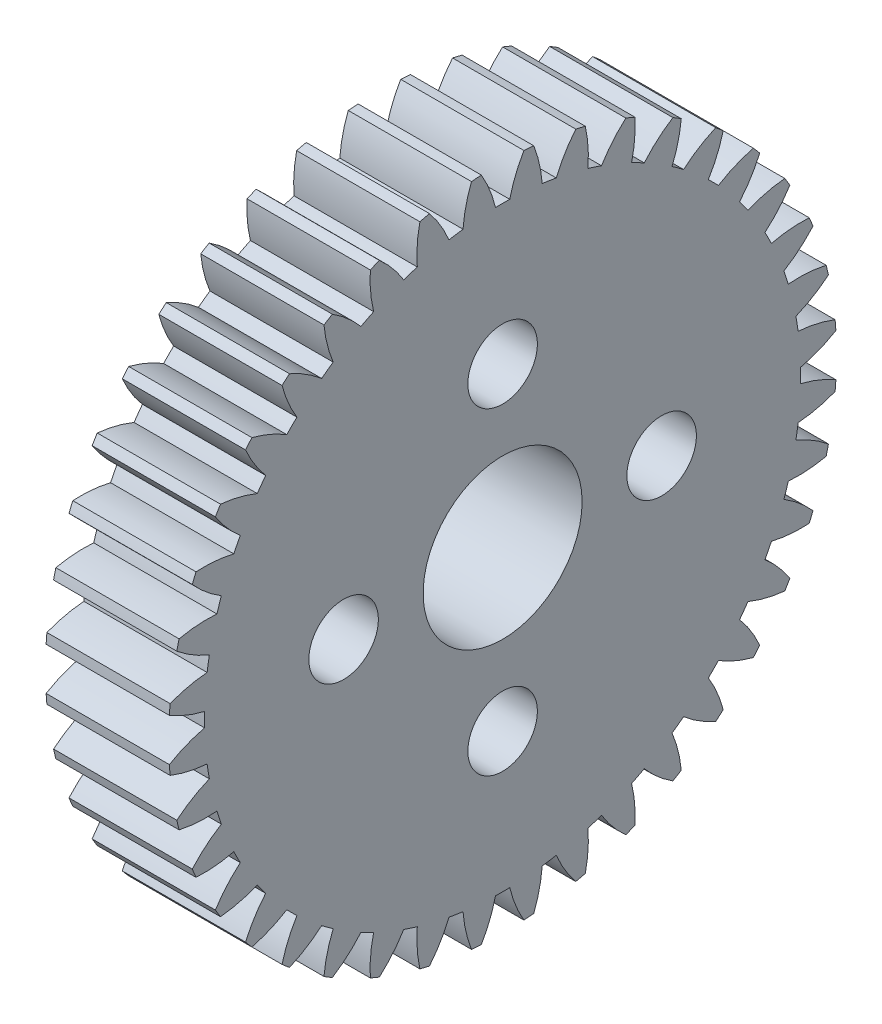
SolidWorks part; units mm, degrees
material "2024 Alloy"
ref_plane "Front Plane" through (0, 0, 0) normal (0, 0, 1) x (1, 0, 0)
ref_plane "Top Plane" through (0, 0, 0) normal (0, 1, 0) x (1, 0, 0)
ref_plane "Right Plane" through (0, 0, 0) normal (1, 0, 0) x (0, 0, -1)
ref_plane "Plane1" through (0, 0, 0) normal (-1, 0, 0) x (0, -1, 0)
sketch "Sketch1" plane through (0, 0, 0) normal (-1, 0, 0) x (0, -1, 0)
  circle A0 centre (0, 0) radius 4
  circle A1 centre (0, 8) radius 1.75
  circle A2 centre (-8, 0) radius 1.75
  circle A3 centre (8, 0) radius 1.75
  circle A4 centre (0, -8) radius 1.75
  arc A5 (-16.2763, -4.1619) -> (-14.3715, -4.2929) centre (-14.8897, 2.0861) ccw
  arc A6 (-14.3715, -4.2929) -> (-14.1501, -4.9743) centre (0, 0) ccw
  arc A7 (-14.1501, -4.9743) -> (-15.6141, -6.1999) centre (-10.8198, -10.4396) ccw
  arc A8 (-15.6141, -6.1999) -> (-15.4249, -6.6568) centre (0, 0) ccw
  arc A9 (-15.4249, -6.6568) -> (-13.523, -6.4883) centre (-15.0327, -0.2689) ccw
  arc A10 (-13.523, -6.4883) -> (-13.1978, -7.1267) centre (0, 0) ccw
  arc A11 (-13.1978, -7.1267) -> (-14.452, -8.5662) centre (-9.0535, -12.0037) ccw
  arc A12 (-14.452, -8.5662) -> (-14.1936, -8.9879) centre (0, 0) ccw
  arc A13 (-14.1936, -8.9879) -> (-12.3415, -8.5239) centre (-14.8055, -2.6172) ccw
  arc A14 (-12.3415, -8.5239) -> (-11.9204, -9.1035) centre (0, 0) ccw
  arc A15 (-11.9204, -9.1035) -> (-12.934, -10.7215) centre (-7.0643, -13.2721) ccw
  arc A16 (-12.934, -10.7215) -> (-12.6128, -11.0976) centre (0, 0) ccw
  arc A17 (-12.6128, -11.0976) -> (-10.8562, -10.3496) centre (-14.2138, -4.9011) ccw
  arc A18 (-10.8562, -10.3496) -> (-10.3496, -10.8562) centre (0, 0) ccw
  arc A19 (-10.3496, -10.8562) -> (-11.0976, -12.6128) centre (-4.9011, -14.2138) ccw
  arc A20 (-11.0976, -12.6128) -> (-10.7215, -12.934) centre (0, 0) ccw
  arc A21 (-10.7215, -12.934) -> (-9.1035, -11.9204) centre (-13.2721, -7.0643) ccw
  arc A22 (-9.1035, -11.9204) -> (-8.5239, -12.3415) centre (0, 0) ccw
  arc A23 (-8.5239, -12.3415) -> (-8.9879, -14.1936) centre (-2.6172, -14.8055) ccw
  arc A24 (-8.9879, -14.1936) -> (-8.5662, -14.452) centre (0, 0) ccw
  arc A25 (-8.5662, -14.452) -> (-7.1267, -13.1978) centre (-12.0037, -9.0535) ccw
  arc A26 (-7.1267, -13.1978) -> (-6.4883, -13.523) centre (0, 0) ccw
  arc A27 (-6.4883, -13.523) -> (-6.6568, -15.4249) centre (-0.2689, -15.0327) ccw
  arc A28 (-6.6568, -15.4249) -> (-6.1999, -15.6141) centre (0, 0) ccw
  arc A29 (-6.1999, -15.6141) -> (-4.9743, -14.1501) centre (-10.4396, -10.8198) ccw
  arc A30 (-4.9743, -14.1501) -> (-4.2929, -14.3715) centre (0, 0) ccw
  arc A31 (-4.2929, -14.3715) -> (-4.1619, -16.2763) centre (2.0861, -14.8897) ccw
  arc A32 (-4.1619, -16.2763) -> (-3.681, -16.3918) centre (0, 0) ccw
  arc A33 (-3.681, -16.3918) -> (-2.6995, -14.7541) centre (-8.6185, -12.3197) ccw
  arc A34 (-2.6995, -14.7541) -> (-1.9919, -14.8662) centre (0, 0) ccw
  arc A35 (-1.9919, -14.8662) -> (-1.5645, -16.727) centre (4.3896, -14.38) ccw
  arc A36 (-1.5645, -16.727) -> (-1.0715, -16.7658) centre (0, 0) ccw
  arc A37 (-1.0715, -16.7658) -> (-0.3582, -14.9947) centre (-6.5851, -13.5163) ccw
  arc A38 (-0.3582, -14.9947) -> (0.3582, -14.9947) centre (0, 0) ccw
  arc A39 (0.3582, -14.9947) -> (1.0715, -16.7658) centre (6.5851, -13.5163) ccw
  arc A40 (1.0715, -16.7658) -> (1.5645, -16.727) centre (0, 0) ccw
  arc A41 (1.5645, -16.727) -> (1.9919, -14.8662) centre (-4.3896, -14.38) ccw
  arc A42 (1.9919, -14.8662) -> (2.6995, -14.7541) centre (0, 0) ccw
  arc A43 (2.6995, -14.7541) -> (3.681, -16.3918) centre (8.6185, -12.3197) ccw
  arc A44 (3.681, -16.3918) -> (4.1619, -16.2763) centre (0, 0) ccw
  arc A45 (4.1619, -16.2763) -> (4.2929, -14.3715) centre (-2.0861, -14.8897) ccw
  arc A46 (4.2929, -14.3715) -> (4.9743, -14.1501) centre (0, 0) ccw
  arc A47 (4.9743, -14.1501) -> (6.1999, -15.6141) centre (10.4396, -10.8198) ccw
  arc A48 (6.1999, -15.6141) -> (6.6568, -15.4249) centre (0, 0) ccw
  arc A49 (6.6568, -15.4249) -> (6.4883, -13.523) centre (0.2689, -15.0327) ccw
  arc A50 (6.4883, -13.523) -> (7.1267, -13.1978) centre (0, 0) ccw
  arc A51 (7.1267, -13.1978) -> (8.5662, -14.452) centre (12.0037, -9.0535) ccw
  arc A52 (8.5662, -14.452) -> (8.9879, -14.1936) centre (0, 0) ccw
  arc A53 (8.9879, -14.1936) -> (8.5239, -12.3415) centre (2.6172, -14.8055) ccw
  arc A54 (8.5239, -12.3415) -> (9.1035, -11.9204) centre (0, 0) ccw
  arc A55 (9.1035, -11.9204) -> (10.7215, -12.934) centre (13.2721, -7.0643) ccw
  arc A56 (10.7215, -12.934) -> (11.0976, -12.6128) centre (0, 0) ccw
  arc A57 (11.0976, -12.6128) -> (10.3496, -10.8562) centre (4.9011, -14.2138) ccw
  arc A58 (10.3496, -10.8562) -> (10.8562, -10.3496) centre (0, 0) ccw
  arc A59 (10.8562, -10.3496) -> (12.6128, -11.0976) centre (14.2138, -4.9011) ccw
  arc A60 (12.6128, -11.0976) -> (12.934, -10.7215) centre (0, 0) ccw
  arc A61 (12.934, -10.7215) -> (11.9204, -9.1035) centre (7.0643, -13.2721) ccw
  arc A62 (11.9204, -9.1035) -> (12.3415, -8.5239) centre (0, 0) ccw
  arc A63 (12.3415, -8.5239) -> (14.1936, -8.9879) centre (14.8055, -2.6172) ccw
  arc A64 (14.1936, -8.9879) -> (14.452, -8.5662) centre (0, 0) ccw
  arc A65 (14.452, -8.5662) -> (13.1978, -7.1267) centre (9.0535, -12.0037) ccw
  arc A66 (13.1978, -7.1267) -> (13.523, -6.4883) centre (0, 0) ccw
  arc A67 (13.523, -6.4883) -> (15.4249, -6.6568) centre (15.0327, -0.2689) ccw
  arc A68 (15.4249, -6.6568) -> (15.6141, -6.1999) centre (0, 0) ccw
  arc A69 (15.6141, -6.1999) -> (14.1501, -4.9743) centre (10.8198, -10.4396) ccw
  arc A70 (14.1501, -4.9743) -> (14.3715, -4.2929) centre (0, 0) ccw
  arc A71 (14.3715, -4.2929) -> (16.2763, -4.1619) centre (14.8897, 2.0861) ccw
  arc A72 (16.2763, -4.1619) -> (16.3918, -3.681) centre (0, 0) ccw
  arc A73 (16.3918, -3.681) -> (14.7541, -2.6995) centre (12.3197, -8.6185) ccw
  arc A74 (14.7541, -2.6995) -> (14.8662, -1.9919) centre (0, 0) ccw
  arc A75 (14.8662, -1.9919) -> (16.727, -1.5645) centre (14.38, 4.3896) ccw
  arc A76 (16.727, -1.5645) -> (16.7658, -1.0715) centre (0, 0) ccw
  arc A77 (16.7658, -1.0715) -> (14.9947, -0.3582) centre (13.5163, -6.5851) ccw
  arc A78 (14.9947, -0.3582) -> (14.9947, 0.3582) centre (0, 0) ccw
  arc A79 (14.9947, 0.3582) -> (16.7658, 1.0715) centre (13.5163, 6.5851) ccw
  arc A80 (16.7658, 1.0715) -> (16.727, 1.5645) centre (0, 0) ccw
  arc A81 (16.727, 1.5645) -> (14.8662, 1.9919) centre (14.38, -4.3896) ccw
  arc A82 (14.8662, 1.9919) -> (14.7541, 2.6995) centre (0, 0) ccw
  arc A83 (14.7541, 2.6995) -> (16.3918, 3.681) centre (12.3197, 8.6185) ccw
  arc A84 (16.3918, 3.681) -> (16.2763, 4.1619) centre (0, 0) ccw
  arc A85 (16.2763, 4.1619) -> (14.3715, 4.2929) centre (14.8897, -2.0861) ccw
  arc A86 (14.3715, 4.2929) -> (14.1501, 4.9743) centre (0, 0) ccw
  arc A87 (14.1501, 4.9743) -> (15.6141, 6.1999) centre (10.8198, 10.4396) ccw
  arc A88 (15.6141, 6.1999) -> (15.4249, 6.6568) centre (0, 0) ccw
  arc A89 (15.4249, 6.6568) -> (13.523, 6.4883) centre (15.0327, 0.2689) ccw
  arc A90 (13.523, 6.4883) -> (13.1978, 7.1267) centre (0, 0) ccw
  arc A91 (13.1978, 7.1267) -> (14.452, 8.5662) centre (9.0535, 12.0037) ccw
  arc A92 (14.452, 8.5662) -> (14.1936, 8.9879) centre (0, 0) ccw
  arc A93 (14.1936, 8.9879) -> (12.3415, 8.5239) centre (14.8055, 2.6172) ccw
  arc A94 (12.3415, 8.5239) -> (11.9204, 9.1035) centre (0, 0) ccw
  arc A95 (11.9204, 9.1035) -> (12.934, 10.7215) centre (7.0643, 13.2721) ccw
  arc A96 (12.934, 10.7215) -> (12.6128, 11.0976) centre (0, 0) ccw
  arc A97 (12.6128, 11.0976) -> (10.8562, 10.3496) centre (14.2138, 4.9011) ccw
  arc A98 (10.8562, 10.3496) -> (10.3496, 10.8562) centre (0, 0) ccw
  arc A99 (10.3496, 10.8562) -> (11.0976, 12.6128) centre (4.9011, 14.2138) ccw
  arc A100 (11.0976, 12.6128) -> (10.7215, 12.934) centre (0, 0) ccw
  arc A101 (10.7215, 12.934) -> (9.1035, 11.9204) centre (13.2721, 7.0643) ccw
  arc A102 (9.1035, 11.9204) -> (8.5239, 12.3415) centre (0, 0) ccw
  arc A103 (8.5239, 12.3415) -> (8.9879, 14.1936) centre (2.6172, 14.8055) ccw
  arc A104 (8.9879, 14.1936) -> (8.5662, 14.452) centre (0, 0) ccw
  arc A105 (8.5662, 14.452) -> (7.1267, 13.1978) centre (12.0037, 9.0535) ccw
  arc A106 (7.1267, 13.1978) -> (6.4883, 13.523) centre (0, 0) ccw
  arc A107 (6.4883, 13.523) -> (6.6568, 15.4249) centre (0.2689, 15.0327) ccw
  arc A108 (6.6568, 15.4249) -> (6.1999, 15.6141) centre (0, 0) ccw
  arc A109 (6.1999, 15.6141) -> (4.9743, 14.1501) centre (10.4396, 10.8198) ccw
  arc A110 (4.9743, 14.1501) -> (4.2929, 14.3715) centre (0, 0) ccw
  arc A111 (4.2929, 14.3715) -> (4.1619, 16.2763) centre (-2.0861, 14.8897) ccw
  arc A112 (4.1619, 16.2763) -> (3.681, 16.3918) centre (0, 0) ccw
  arc A113 (3.681, 16.3918) -> (2.6995, 14.7541) centre (8.6185, 12.3197) ccw
  arc A114 (2.6995, 14.7541) -> (1.9919, 14.8662) centre (0, 0) ccw
  arc A115 (1.9919, 14.8662) -> (1.5645, 16.727) centre (-4.3896, 14.38) ccw
  arc A116 (1.5645, 16.727) -> (1.0715, 16.7658) centre (0, 0) ccw
  arc A117 (1.0715, 16.7658) -> (0.3582, 14.9947) centre (6.5851, 13.5163) ccw
  arc A118 (0.3582, 14.9947) -> (-0.3582, 14.9947) centre (0, 0) ccw
  arc A119 (-0.3582, 14.9947) -> (-1.0715, 16.7658) centre (-6.5851, 13.5163) ccw
  arc A120 (-1.0715, 16.7658) -> (-1.5645, 16.727) centre (0, 0) ccw
  arc A121 (-1.5645, 16.727) -> (-1.9919, 14.8662) centre (4.3896, 14.38) ccw
  arc A122 (-1.9919, 14.8662) -> (-2.6995, 14.7541) centre (0, 0) ccw
  arc A123 (-2.6995, 14.7541) -> (-3.681, 16.3918) centre (-8.6185, 12.3197) ccw
  arc A124 (-3.681, 16.3918) -> (-4.1619, 16.2763) centre (0, 0) ccw
  arc A125 (-4.1619, 16.2763) -> (-4.2929, 14.3715) centre (2.0861, 14.8897) ccw
  arc A126 (-4.2929, 14.3715) -> (-4.9743, 14.1501) centre (0, 0) ccw
  arc A127 (-4.9743, 14.1501) -> (-6.1999, 15.6141) centre (-10.4396, 10.8198) ccw
  arc A128 (-6.1999, 15.6141) -> (-6.6568, 15.4249) centre (0, 0) ccw
  arc A129 (-6.6568, 15.4249) -> (-6.4883, 13.523) centre (-0.2689, 15.0327) ccw
  arc A130 (-6.4883, 13.523) -> (-7.1267, 13.1978) centre (0, 0) ccw
  arc A131 (-7.1267, 13.1978) -> (-8.5662, 14.452) centre (-12.0037, 9.0535) ccw
  arc A132 (-8.5662, 14.452) -> (-8.9879, 14.1936) centre (0, 0) ccw
  arc A133 (-8.9879, 14.1936) -> (-8.5239, 12.3415) centre (-2.6172, 14.8055) ccw
  arc A134 (-8.5239, 12.3415) -> (-9.1035, 11.9204) centre (0, 0) ccw
  arc A135 (-9.1035, 11.9204) -> (-10.7215, 12.934) centre (-13.2721, 7.0643) ccw
  arc A136 (-10.7215, 12.934) -> (-11.0976, 12.6128) centre (0, 0) ccw
  arc A137 (-11.0976, 12.6128) -> (-10.3496, 10.8562) centre (-4.9011, 14.2138) ccw
  arc A138 (-10.3496, 10.8562) -> (-10.8562, 10.3496) centre (0, 0) ccw
  arc A139 (-10.8562, 10.3496) -> (-12.6128, 11.0976) centre (-14.2138, 4.9011) ccw
  arc A140 (-12.6128, 11.0976) -> (-12.934, 10.7215) centre (0, 0) ccw
  arc A141 (-12.934, 10.7215) -> (-11.9204, 9.1035) centre (-7.0643, 13.2721) ccw
  arc A142 (-11.9204, 9.1035) -> (-12.3415, 8.5239) centre (0, 0) ccw
  arc A143 (-12.3415, 8.5239) -> (-14.1936, 8.9879) centre (-14.8055, 2.6172) ccw
  arc A144 (-14.1936, 8.9879) -> (-14.452, 8.5662) centre (0, 0) ccw
  arc A145 (-14.452, 8.5662) -> (-13.1978, 7.1267) centre (-9.0535, 12.0037) ccw
  arc A146 (-13.1978, 7.1267) -> (-13.523, 6.4883) centre (0, 0) ccw
  arc A147 (-13.523, 6.4883) -> (-15.4249, 6.6568) centre (-15.0327, 0.2689) ccw
  arc A148 (-15.4249, 6.6568) -> (-15.6141, 6.1999) centre (0, 0) ccw
  arc A149 (-15.6141, 6.1999) -> (-14.1501, 4.9743) centre (-10.8198, 10.4396) ccw
  arc A150 (-14.1501, 4.9743) -> (-14.3715, 4.2929) centre (0, 0) ccw
  arc A151 (-14.3715, 4.2929) -> (-16.2763, 4.1619) centre (-14.8897, -2.0861) ccw
  arc A152 (-16.2763, 4.1619) -> (-16.3918, 3.681) centre (0, 0) ccw
  arc A153 (-16.3918, 3.681) -> (-14.7541, 2.6995) centre (-12.3197, 8.6185) ccw
  arc A154 (-14.7541, 2.6995) -> (-14.8662, 1.9919) centre (0, 0) ccw
  arc A155 (-14.8662, 1.9919) -> (-16.727, 1.5645) centre (-14.38, -4.3896) ccw
  arc A156 (-16.727, 1.5645) -> (-16.7658, 1.0715) centre (0, 0) ccw
  arc A157 (-16.7658, 1.0715) -> (-14.9947, 0.3582) centre (-13.5163, 6.5851) ccw
  arc A158 (-14.9947, 0.3582) -> (-14.9947, -0.3582) centre (0, 0) ccw
  arc A159 (-14.9947, -0.3582) -> (-16.7658, -1.0715) centre (-13.5163, -6.5851) ccw
  arc A160 (-16.7658, -1.0715) -> (-16.727, -1.5645) centre (0, 0) ccw
  arc A161 (-16.727, -1.5645) -> (-14.8662, -1.9919) centre (-14.38, 4.3896) ccw
  arc A162 (-14.8662, -1.9919) -> (-14.7541, -2.6995) centre (0, 0) ccw
  arc A163 (-14.7541, -2.6995) -> (-16.3918, -3.681) centre (-12.3197, -8.6185) ccw
  arc A164 (-16.3918, -3.681) -> (-16.2763, -4.1619) centre (0, 0) ccw
extrude "Boss-Extrude1" add sketch "Sketch1" against normal blind 6.2
